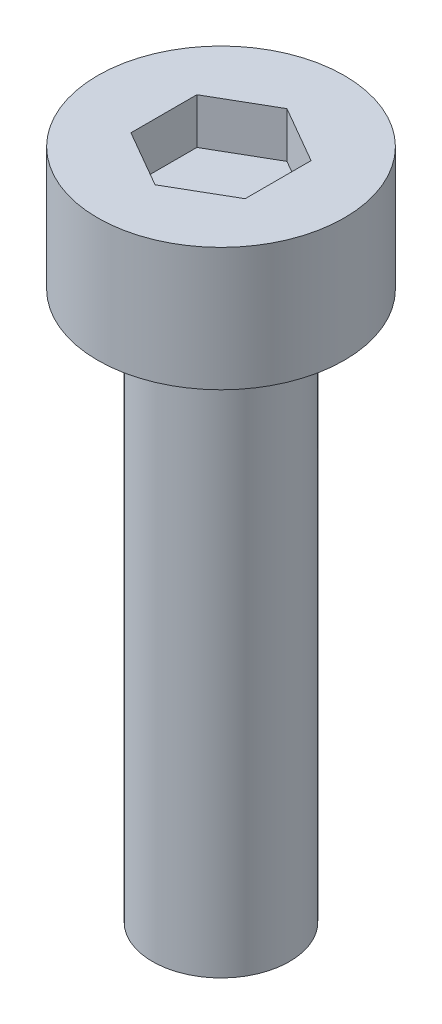
SolidWorks part; units mm, degrees
ref_plane "Front Plane" through (0, 0, 0) normal (0, 0, 1) x (1, 0, 0)
ref_plane "Top Plane" through (0, 0, 0) normal (0, 1, 0) x (1, 0, 0)
ref_plane "Right Plane" through (0, 0, 0) normal (1, 0, 0) x (0, 0, -1)
sketch "Sketch1" plane through (0, 0, 0) normal (0, 1, 0) x (1, 0, 0)
  circle A0 centre (0, 0) radius 2.7
extrude "Boss-Extrude1" add sketch "Sketch1" along normal blind 2.7
sketch "Sketch2" plane through (0, 2.7, 0) normal (0, 1, 0) x (1, 0, 0)
  line L1 (0, 1.4434) -> (-1.25, 0.7217)
  line L2 (-1.25, 0.7217) -> (-1.25, -0.7217)
  line L3 (-1.25, -0.7217) -> (0, -1.4434)
  line L4 (0, -1.4434) -> (1.25, -0.7217)
  line L5 (1.25, -0.7217) -> (1.25, 0.7217)
  line L6 (1.25, 0.7217) -> (0, 1.4434)
  circle A0 centre (0, 0) radius 1.25 construction
extrude "Cut-Extrude1" cut sketch "Sketch2" against normal blind 1
sketch "Sketch3" plane through (0, 0, 0) normal (0, -1, 0) x (1, 0, 0)
  circle A0 centre (0, 0) radius 1.5
extrude "Boss-Extrude2" add sketch "Sketch3" along normal blind 12
